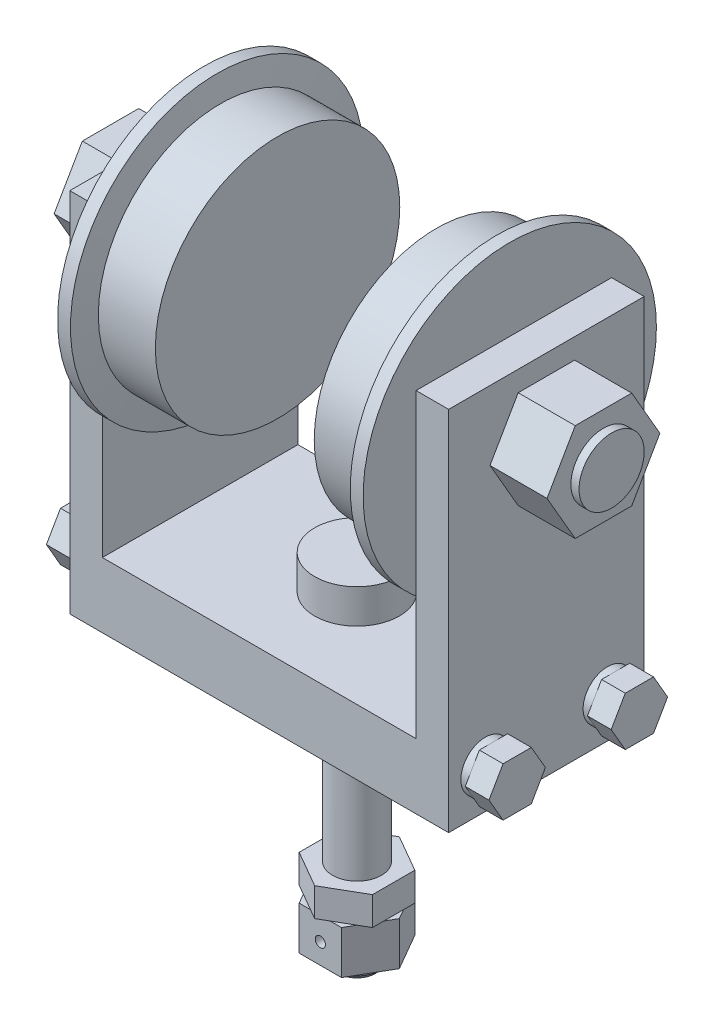
SolidWorks part; units mm, degrees
ref_plane "Front" through (0, 0, 0) normal (0, 0, 1) x (1, 0, 0)
ref_plane "Top" through (0, 0, 0) normal (0, 1, 0) x (1, 0, 0)
ref_plane "Right" through (0, 0, 0) normal (1, 0, 0) x (0, 0, -1)
ref_plane "Z PLANE" through (0, 0, 0) normal (0, 0, 1) x (1, 0, 0)
ref_plane "YOKE BOTTOM" through (0, 0, 0) normal (0, 1, 0) x (-1, 0, 0)
ref_plane "X PLANE" through (0, 0, 0) normal (1, 0, 0) x (0, 0, -1)
sketch "YOKE CROSS SECTION" plane through (0, 0, 0) normal (1, 0, 0) x (0, 0, -1)
  line L0 (0, 0) -> (0, 57.0916) construction
  line L1 (0, 72.125) -> (0, -72.125) construction
  line L2 (-38.1, 0) -> (38.1, 0)
  line L3 (69.1602, 0) -> (-69.1602, 0) construction
  line L4 (38.1, 0) -> (38.1, 25.4)
  line L5 (-38.1, 0) -> (-38.1, 25.4)
  line L6 (38.1, 25.4) -> (-38.1, 25.4)
  point P12 (0, 25.4)
  dimension "D1" = 25.4
  dimension "D2" = 76.2
ref_plane "1/2 YOKE LENGTH (A)" through (61.1187, 0, 0) normal (1, 0, 0) x (0, 0, -1)
extrude "YOKE" add sketch "YOKE CROSS SECTION" along normal up to surface (61.1188 mm away) up to plane "1/2 YOKE LENGTH (A)"
sketch "SIDEPLATE PROFILE" plane through (61.1187, 0, 0) normal (1, 0, 0) x (0, 0, -1)
  line L0 (0, 0) -> (0, 74.7424) construction
  line L1 (0, 72.125) -> (0, -72.125) construction
  line L2 (-38.1, 0) -> (38.1, 0)
  line L3 (38.1, 0) -> (38.1, 142.875)
  line L4 (-38.1, 0) -> (-38.1, 142.875)
  line L5 (38.1, 142.875) -> (-38.1, 142.875)
  point P11 (0, 142.875)
  dimension "D1" = 142.875
ref_plane "WHEEL HEIGHT" through (0, 115.8875, 0) normal (0, 1, 0) x (-1, 0, 0)
ref_plane "SCREW LOCATION X" through (0, 0, 23.8125) normal (0, 0, 1) x (1, 0, 0)
ref_plane "SCREW LOCATION Y" through (0, 15.5632, 0) normal (0, 1, 0) x (-1, 0, 0)
extrude "SIDEPLATE" add sketch "SIDEPLATE PROFILE" along normal blind 12.7
sketch "WHEEL PIN NUT PROFILE" plane through (73.8188, 0, 0) normal (1, 0, 0) x (0, 0, -1)
  line L0 (0, 72.125) -> (0, -72.125) construction
  line L1 (21.997, 115.8875) -> (10.9985, 134.9375)
  line L2 (10.9985, 134.9375) -> (-10.9985, 134.9375)
  line L3 (-10.9985, 134.9375) -> (-21.997, 115.8875)
  line L4 (-21.997, 115.8875) -> (-10.9985, 96.8375)
  line L5 (-10.9985, 96.8375) -> (10.9985, 96.8375)
  line L6 (10.9985, 96.8375) -> (21.997, 115.8875)
  line L7 (69.1602, 115.8875) -> (-69.1602, 115.8875) construction
  circle A0 centre (0, 115.8875) radius 19.05 construction
  dimension "D1" = 38.1
extrude "WHEEL PIN NUT" add sketch "WHEEL PIN NUT PROFILE" along normal blind 22.225
sketch "WHEEL PIN PROJECTION PROFILE" plane through (96.0438, 0, 0) normal (1, 0, 0) x (0, 0, -1)
  line L0 (0, 72.125) -> (0, -72.125) construction
  line L1 (69.1602, 115.8875) -> (-69.1602, 115.8875) construction
  circle A0 centre (0, 115.8875) radius 12.7
  dimension "D1" = 25.4
extrude "WHEEL PIN PROJECTION" add sketch "WHEEL PIN PROJECTION PROFILE" along normal blind 3.175
sketch "LOCKNUTS PROFILE" plane through (73.8188, 0, 0) normal (1, 0, 0) x (0, 0, -1)
  line L0 (-23.8125, 84.8167) -> (-23.8125, -84.8167) construction
  line L1 (50, 15.5632) -> (-50, 15.5632) construction
  circle A0 centre (-23.8125, 15.5632) radius 9.525
  dimension "D1" = 19.05
extrude "LOCKNUTS" add sketch "LOCKNUTS PROFILE" along normal blind 3.175
sketch "SCREWS PROFILE" plane through (76.9938, 0, 0) normal (1, 0, 0) x (0, 0, -1)
  line L0 (50, 15.5632) -> (-50, 15.5632) construction
  line L1 (-12.814, 15.5632) -> (-18.3132, 25.0882)
  line L2 (-18.3132, 25.0882) -> (-29.3118, 25.0882)
  line L3 (-29.3118, 25.0882) -> (-34.811, 15.5632)
  line L4 (-34.811, 15.5632) -> (-29.3118, 6.0382)
  line L5 (-29.3118, 6.0382) -> (-18.3132, 6.0382)
  line L6 (-18.3132, 6.0382) -> (-12.814, 15.5632)
  line L7 (-23.8125, 84.8167) -> (-23.8125, -84.8167) construction
  circle A0 centre (-23.8125, 15.5632) radius 9.525 construction
  dimension "D1" = 19.05
extrude "SCREWS" add sketch "SCREWS PROFILE" along normal blind 9.2456
sketch "PROFILE" plane through (0, 25.4, 0) normal (0, 1, 0) x (-1, 0, 0)
  line L0 (72.125, 0) -> (-72.125, 0) construction
  line L1 (0, 83.2389) -> (0, -83.2389) construction
  circle A0 centre (0, 0) radius 16.4973
  dimension "D1" = 32.9946
extrude "KING BOLT HEAD" add sketch "PROFILE" along normal blind 13.3096
mirror "Mirror1" about plane through (0, 0, 0) normal (0, 0, 1) of "SCREWS", "LOCKNUTS"
mirror "Mirror5" about plane through (0, 0, 0) normal (1, 0, 0) of bodies 112
ref_plane "TOP OF NUT" through (0, -65.5896, 0) normal (0, 1, 0) x (-1, 0, 0)
sketch "DIA." plane through (0, 0, 0) normal (0, -1, 0) x (1, 0, 0)
  line L0 (72.125, 0) -> (-72.125, 0) construction
  line L1 (0, -83.2389) -> (0, 83.2389) construction
  circle A0 centre (0, 0) radius 9.525
  dimension "D1" = 19.05
extrude "KING BOLT" add sketch "DIA." along normal up to surface (65.5896 mm away) up to plane "TOP OF NUT"
sketch "KING BOLT JAN NUT PROFILE" plane through (0, -65.5896, 0) normal (0, -1, 0) x (1, 0, 0)
  line L0 (72.125, 0) -> (-72.125, 0) construction
  line L1 (0, -16.4978) -> (14.2875, -8.2489)
  line L2 (14.2875, -8.2489) -> (14.2875, 8.2489)
  line L3 (14.2875, 8.2489) -> (0, 16.4978)
  line L4 (0, 16.4978) -> (-14.2875, 8.2489)
  line L5 (-14.2875, 8.2489) -> (-14.2875, -8.2489)
  line L6 (-14.2875, -8.2489) -> (0, -16.4978)
  line L7 (0, -83.2389) -> (0, 83.2389) construction
  circle A0 centre (0, 0) radius 14.2875 construction
  dimension "D1" = 28.575
extrude "KING BOLT JAM NUT" add sketch "KING BOLT JAN NUT PROFILE" along normal blind 11.1125
sketch "KING BOLT NUT PROFILE" plane through (0, -76.7021, 0) normal (0, -1, 0) x (1, 0, 0)
  line L1 (16.4978, 0) -> (8.2489, 14.2875)
  line L2 (8.2489, 14.2875) -> (-8.2489, 14.2875)
  line L3 (-8.2489, 14.2875) -> (-16.4978, 0)
  line L4 (-16.4978, 0) -> (-8.2489, -14.2875)
  line L5 (-8.2489, -14.2875) -> (8.2489, -14.2875)
  line L6 (8.2489, -14.2875) -> (16.4978, 0)
  line L10 (0, -83.2389) -> (0, 83.2389) construction
  line L11 (72.125, 0) -> (-72.125, 0) construction
  circle A0 centre (0, 0) radius 14.2875 construction
  dimension "D1" = 28.575
extrude "KING BOLT NUT" add sketch "KING BOLT NUT PROFILE" along normal blind 16.891
sketch "Sketch5" plane through (0, -93.5931, 0) normal (0, -1, 0) x (1, 0, 0)
  circle A0 centre (0, 0) radius 9.525 construction
  circle A1 centre (0, 0) radius 9.525
extrude "EXTENDED KING BOLT" add sketch "Sketch5" along normal blind 6.35
chamfer "Chamfer1" distance 2.3812 angle 45 1 edges at (0, -99.9431, -9.525)
ref_plane "MOUNTING REF PLANE" through (0, -34.925, 0) normal (0, 1, 0) x (-1, 0, 0)
sketch "Sketch7" plane through (0, 0, 0) normal (0, 0, 1) x (1, 0, 0)
  line L0 (59.5312, 173.0375) -> (54.5199, 173.0375)
  line L1 (30.9562, 115.8875) -> (61.1187, 115.8875)
  line L2 (30.9562, 163.5125) -> (30.9562, 115.8875)
  line L3 (53.1812, 163.5125) -> (54.5199, 173.0375)
  line L4 (53.1812, 163.5125) -> (30.9562, 163.5125)
  line L5 (59.5312, 131.7625) -> (59.5312, 173.0375)
  line L6 (61.1187, 115.8875) -> (61.1187, 131.7625)
  line L7 (59.5312, 131.7625) -> (61.1187, 131.7625)
  line L8 (69.1602, 115.8875) -> (-69.1602, 115.8875) construction
  line L9 (61.1187, -75.0522) -> (61.1187, 75.0522) construction
  dimension "D1" = 15.875
  dimension "D2" = 30.1625
  dimension "D6" = 57.15
  dimension "D3" = 47.625
  dimension "D4" = 22.225
  dimension "D5" = 23.5637
  dimension "D7" = 1.5875
revolve "WHEEL" add sketch "Sketch7" angle 360 about axis through (99.2188, 115.8875, 0) along (-1, 0, 0)
mirror "Mirror6" about plane through (0, 0, 0) normal (1, 0, 0) of "WHEEL"
sketch "Sketch8" plane through (0, 0, 14.2875) normal (0, 0, 1) x (1, 0, 0)
  line L0 (0, -83.2389) -> (0, 83.2389) construction
  circle A0 centre (0, -85.6556) radius 1.9844
  dimension "D2" = 3.9688
  dimension "D1" = 7.9375
extrude "COTTER PIN HOLE" cut sketch "Sketch8" against normal up to next
sketch "Sketch9" plane through (0, 0, 0) normal (0, -1, 0) x (1, 0, 0)
  circle A0 centre (0, 0) radius 25.4
  circle A1 centre (0, 0) radius 30.1625
  dimension "D1" = 50.8
  dimension "D2" = 60.325
extrude "SPACER" [suppressed] add sketch "Sketch9" along normal blind 12.7
ref_plane "TREAD OF TRACK" through (0, 68.2625, 0) normal (0, 1, 0) x (-1, 0, 0)
